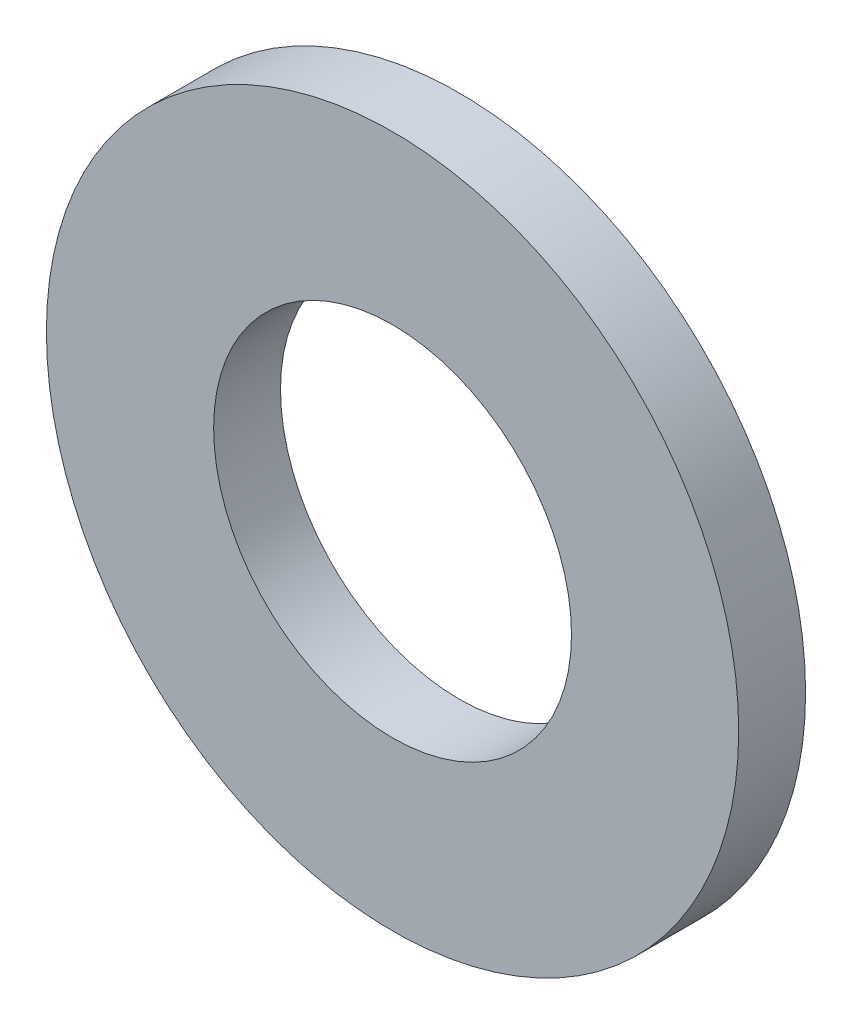
SolidWorks part; units mm, degrees
ref_plane "Front Plane" through (0, 0, 0) normal (0, 0, 1) x (1, 0, 0)
ref_plane "Top Plane" through (0, 0, 0) normal (0, 1, 0) x (1, 0, 0)
ref_plane "Right Plane" through (0, 0, 0) normal (1, 0, 0) x (0, 0, -1)
sketch "Sketch1" plane through (0, 0, 0) normal (0, 0, 1) x (1, 0, 0)
  circle A0 centre (0, 0) radius 10.35
  circle A1 centre (0, 0) radius 5.35
  dimension "D1" = 20.7
  dimension "D2" = 10.7
extrude "Boss-Extrude1" add sketch "Sketch1" along normal blind 2
